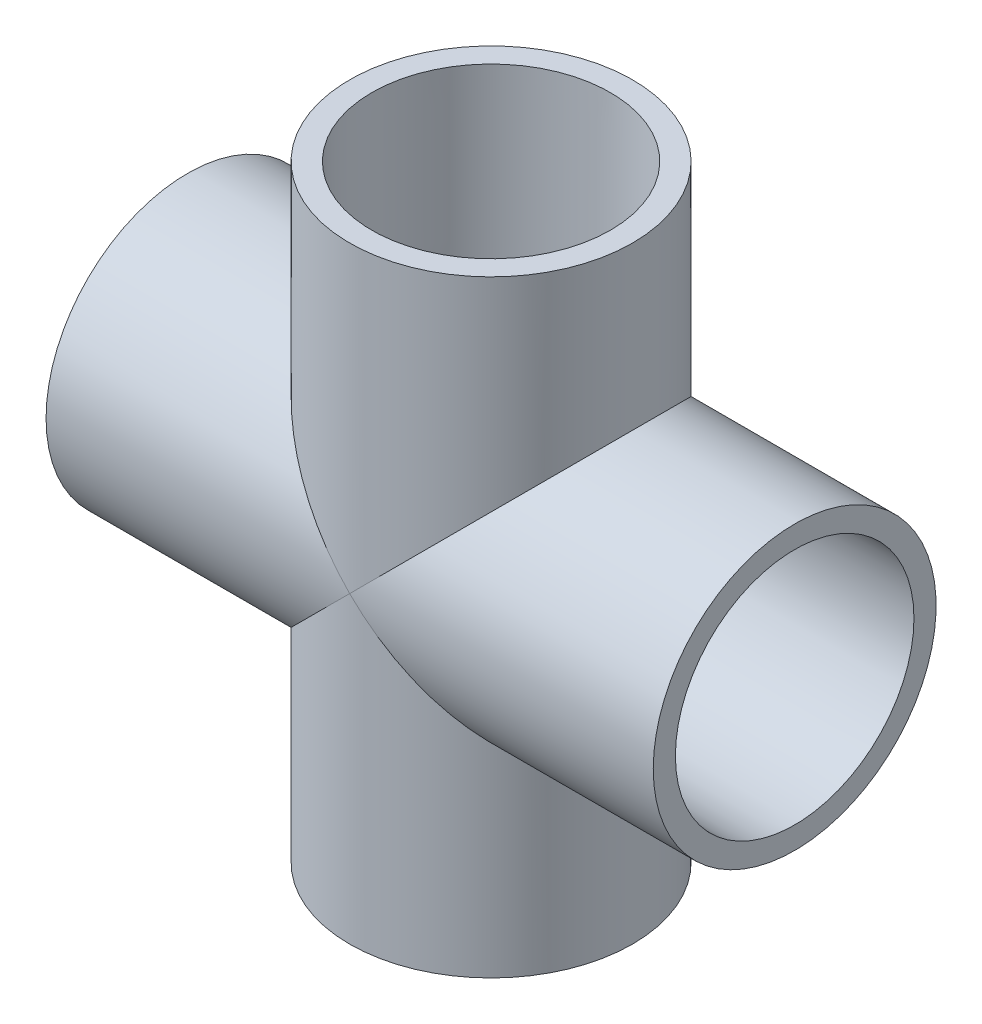
SolidWorks part; units mm, degrees
ref_plane "Front Plane" through (0, 0, 0) normal (0, 0, 1) x (1, 0, 0)
ref_plane "Top Plane" through (0, 0, 0) normal (0, 1, 0) x (1, 0, 0)
ref_plane "Right Plane" through (0, 0, 0) normal (1, 0, 0) x (0, 0, -1)
sketch "Sketch0" plane through (0, 0, 0) normal (0, 0, 1) x (1, 0, 0)
  line L0 (-53.975, 0) -> (0, 0) construction
  line L1 (0, 0) -> (0, 53.975) construction
  line L2 (-22.225, 0) -> (0, 0) construction
  line L3 (0, 0) -> (0, 22.225) construction
  line L4 (-53.975, 25.146) -> (-53.975, -25.146) construction
  line L5 (-22.225, 21.0185) -> (-53.975, 21.209) construction
  line L6 (-22.225, 21.0185) -> (-22.225, -21.0185) construction
  line L7 (-22.225, -21.0185) -> (-53.975, -21.209) construction
  line L8 (-53.975, 21.209) -> (-53.975, -21.209) construction
  line L9 (-25.146, 53.975) -> (25.146, 53.975) construction
  line L10 (-21.209, 53.975) -> (21.209, 53.975) construction
  line L11 (21.209, 53.975) -> (21.0185, 22.225) construction
  line L12 (21.0185, 22.225) -> (-21.0185, 22.225) construction
  line L13 (-21.0185, 22.225) -> (-21.209, 53.975) construction
  line L14 (-22.225, 17.526) -> (-22.225, -17.526) construction
  line L15 (-53.975, 0) -> (-22.225, 0) construction
  line L16 (0, 53.975) -> (0, 22.225) construction
  line L17 (0, 0) -> (22.225, 0) construction
  line L18 (-17.526, 22.225) -> (17.526, 22.225) construction
  line L19 (22.225, 0) -> (53.975, 0) construction
  line L20 (0, 0) -> (0, -22.225) construction
  line L21 (0, -22.225) -> (0, -53.975) construction
  dimension "H" = 53.975
  dimension "G" = 22.225
  dimension "M" = 50.292
  dimension "OD A" = 42.418
  dimension "OD B" = 42.037
  dimension "ID" = 35.052
sketch "Sketch1" plane through (0, 0, 0) normal (0, 0, 1) x (1, 0, 0)
  line L0 (-53.975, 0) -> (0, 0) construction
  line L1 (-53.975, 0) -> (0, 0) construction
  line L2 (0, 0) -> (0, -25.146) construction
  line L3 (-53.975, -25.146) -> (-22.225, -25.146)
  line L4 (-53.975, -25.146) -> (-53.975, -21.209)
  line L5 (-53.975, -21.209) -> (-22.225, -21.0185)
  line L6 (-22.225, -25.146) -> (-22.225, -21.0185)
  line L7 (-22.225, -25.146) -> (0, -25.146) construction
  line L8 (53.975, -21.209) -> (22.225, -21.0185)
  line L9 (53.975, -25.146) -> (53.975, -21.209)
  line L10 (22.225, -25.146) -> (22.225, -21.0185)
  line L11 (53.975, -25.146) -> (22.225, -25.146)
revolve "Revolve1" add sketch "Sketch1" angle 360 about L1
sketch "Sketch2" plane through (0, 0, 0) normal (0, 0, 1) x (1, 0, 0)
  line L0 (21.209, 53.975) -> (21.0185, 22.225)
  line L1 (21.0185, 22.225) -> (25.146, 22.225)
  line L2 (25.146, 22.225) -> (25.146, 53.975)
  line L3 (25.146, 53.975) -> (21.209, 53.975)
  line L4 (0, 0) -> (0, 53.975) construction
  line L5 (0, 0) -> (0, 53.975) construction
  line L6 (0, 0) -> (22.225, 0) construction
  line L7 (25.146, -53.975) -> (21.209, -53.975)
  line L8 (25.146, -22.225) -> (25.146, -53.975)
  line L9 (21.0185, -22.225) -> (25.146, -22.225)
  line L10 (21.209, -53.975) -> (21.0185, -22.225)
revolve "Revolve2" add sketch "Sketch2" angle 360 about L5
sketch "Sketch3" plane through (-22.225, 0, 0) normal (1, 0, 0) x (0, 0, -1)
  circle A0 centre (0, 0) radius 17.526
  circle A1 centre (0, 0) radius 25.146
sketch "Sketch4" plane through (-22.225, 0, 0) normal (1, 0, 0) x (0, 0, -1)
  circle A0 centre (0, 0) radius 25.146 construction
  circle A1 centre (0, 0) radius 25.146
extrude "Boss-Extrude1" add sketch "Sketch4" along normal up to vertex
sketch "Sketch5" plane through (0, 22.225, 0) normal (0, -1, 0) x (1, 0, 0)
  circle A0 centre (0, 0) radius 25.146 construction
  circle A1 centre (0, 0) radius 25.146
extrude "Boss-Extrude2" add sketch "Sketch5" along normal up to vertex (44.45 mm away) up to point (0, -22.225, 0)
sketch "Sketch6" plane through (0, 0, 0) normal (0, 0, 1) x (1, 0, 0)
  line L0 (-53.975, -21.209) -> (-22.225, -21.0185)
  line L1 (-22.225, -21.0185) -> (-22.225, -17.526)
  line L2 (-22.225, -17.526) -> (22.225, -17.526)
  line L3 (22.225, -17.4186) -> (22.225, 17.4186) construction
  line L4 (0, -17.526) -> (0, 0) construction
  line L5 (22.225, -21.0185) -> (22.225, -17.526)
  line L6 (53.975, -21.209) -> (53.975, 21.209) construction
  line L7 (53.975, -25.146) -> (53.975, 25.146) construction
  line L8 (53.975, -21.209) -> (53.975, 0)
  line L9 (53.975, 0) -> (-53.975, 0)
  line L10 (-53.975, 0) -> (-53.975, -21.209)
  line L11 (53.975, -21.209) -> (22.225, -21.0185)
revolve "Cut-Revolve1" cut sketch "Sketch6" angle 360 about L9
sketch "Sketch7" plane through (0, 0, 0) normal (0, 0, 1) x (1, 0, 0)
  line L0 (21.209, 53.975) -> (21.0185, 22.225)
  line L1 (21.0185, 22.225) -> (17.526, 22.225)
  line L2 (17.526, 22.225) -> (17.526, -22.225)
  line L4 (17.526, 0) -> (0, 0) construction
  line L5 (0, 53.975) -> (0, -53.975)
  line L6 (-25.146, 53.975) -> (25.146, 53.975) construction
  line L7 (0, 53.975) -> (21.209, 53.975)
  line L8 (21.0185, -22.225) -> (17.526, -22.225)
  line L9 (21.209, -53.975) -> (21.0185, -22.225)
  line L10 (0, 0) -> (22.225, 0) construction
  line L11 (0, -53.975) -> (21.209, -53.975)
revolve "Cut-Revolve2" cut sketch "Sketch7" angle 360 about L5
